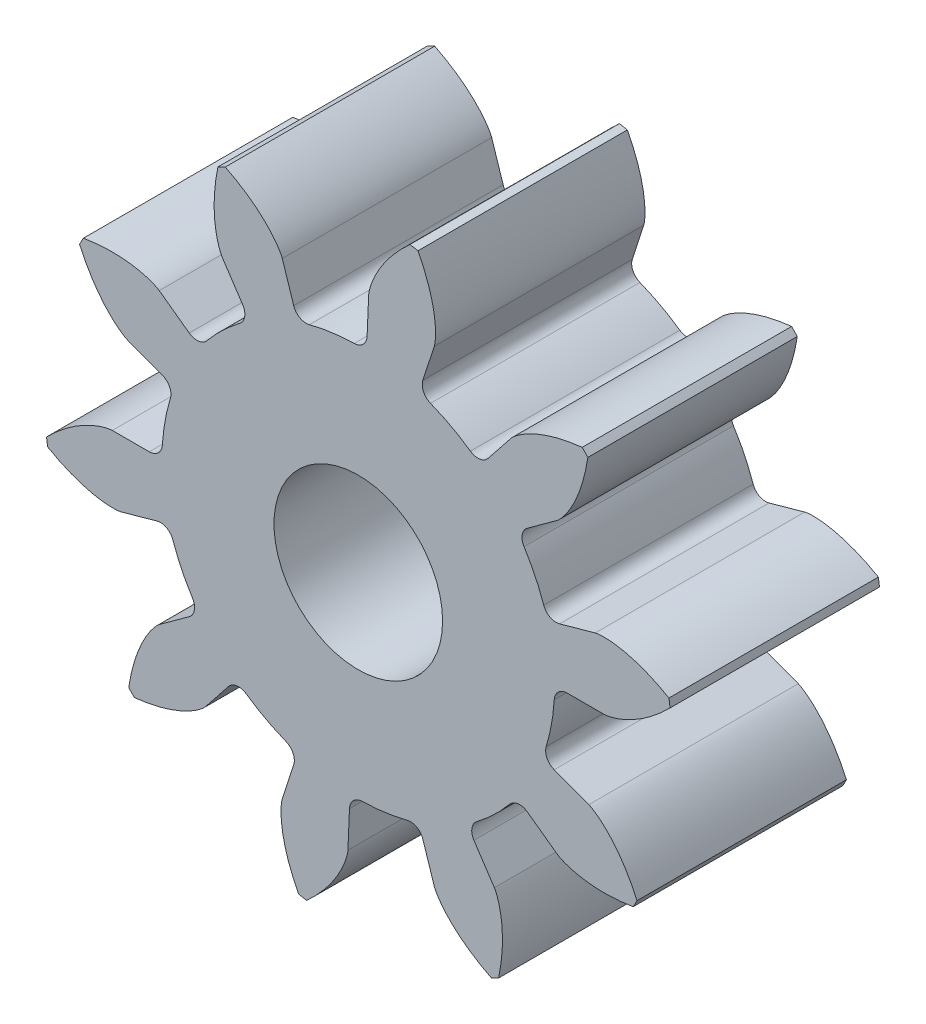
SolidWorks part; units mm, degrees
ref_plane "Front Plane" through (0, 0, 0) normal (0, 0, 1) x (1, 0, 0)
ref_plane "Top Plane" through (0, 0, 0) normal (0, 1, 0) x (1, 0, 0)
ref_plane "Right Plane" through (0, 0, 0) normal (1, 0, 0) x (0, 0, -1)
sketch "Sketch1" plane through (0, 0, 0) normal (0, 0, 1) x (1, 0, 0)
  line L0 (11.7462, 0) -> (9.375, 0)
  line L1 (14.8615, 2.0335) -> (-14.8615, -2.0335)
  line L2 (0, 0) -> (12.4986, 0.1863) construction
  circle A0 centre (0, 0) radius 11.7462 construction
  circle A1 centre (0, 0) radius 15
  circle A2 centre (0, 0) radius 9.375
  circle A3 centre (0, 0) radius 12.5 construction
  spline S0 degree 4 poles (11.7462, 0) (11.7548, 0.0002) (11.7792, 0.0013) (11.8251, 0.0056) (11.8997, 0.0157) (11.9942, 0.0334) (12.1154, 0.0615) (12.2568, 0.1013) (12.4106, 0.1522) (12.5757, 0.215) (12.7384, 0.2842) (12.8986, 0.3593) (13.0561, 0.4395) (13.2442, 0.5429) (13.4661, 0.6756) (13.7194, 0.8429) (13.9992, 1.0471) (14.2756, 1.27) (14.5402, 1.5014) (14.7983, 1.7485) (15.0415, 1.9969) (15.284, 2.2678) (15.5027, 2.5246) (15.7358, 2.8258) (15.9205, 3.0729) (16.1508, 3.4126) (16.2828, 3.6172) (16.4326, 3.8613) (16.4966, 3.972) (16.5361, 4.0402) knots 0 0 0 0 0 0.005377 0.015084 0.028532 0.04661 0.064855 0.092111 0.119476 0.146842 0.174209 0.201575 0.228941 0.256307 0.307035 0.361767 0.4165 0.471232 0.525964 0.580697 0.635429 0.690161 0.744894 0.799626 0.854358 0.909091 0.954545 1 1 1 1 1 construction
  spline S1 degree 4 poles (11.7462, 0) (11.7548, 0.0002) (11.7792, 0.0013) (11.8251, 0.0056) (11.8997, 0.0157) (11.9942, 0.0334) (12.1154, 0.0615) (12.2568, 0.1013) (12.4106, 0.1522) (12.5757, 0.215) (12.7384, 0.2842) (12.8986, 0.3593) (13.0561, 0.4395) (13.2442, 0.5429) (13.4661, 0.6756) (13.7194, 0.8429) (13.9992, 1.0471) (14.2756, 1.27) (14.5402, 1.5014) (14.7983, 1.7485) (15.0415, 1.9969) (15.284, 2.2678) (15.5027, 2.5246) (15.7358, 2.8258) (15.9205, 3.0729) (16.1009, 3.3389) (16.1871, 3.47) (16.2305, 3.5376) knots 0 0 0 0 0 0.005377 0.015084 0.028532 0.04661 0.064855 0.092111 0.119476 0.146842 0.174209 0.201575 0.228941 0.256307 0.307035 0.361767 0.4165 0.471232 0.525964 0.580697 0.635429 0.690161 0.744894 0.799626 0.854358 0.909091 0.909091 0.909091 0.909091 0.909091
  dimension "D1" = 23.4923
  dimension "D2" = 30
  dimension "D3" = 18.75
  dimension "D5" = 25
  dimension "D4" = 6.937
extrude "Boss-Extrude3" add sketch "Sketch1" along normal blind 10 contours L1 A2 | A2 L1 | L0 S1 A1 L1 A2
mirror "Mirror2" about plane through (0, 0, 10) normal (0.1356, -0.9908, 0) of "Boss-Extrude3"
fillet "Fillet1" radius 0.625 2 edges at (9.0304, 2.5184, 5) (9.375, 0, 5)
pattern_circular "CirPattern8" count 10 over 360 about axis through (0, 0, 10) along (0, 0, -1) of "Boss-Extrude3", "Mirror2", "Fillet1"
sketch "Sketch3" plane through (0, 0, 10) normal (0, 0, 1) x (1, 0, 0)
  circle A0 centre (0, 0) radius 4.025
  dimension "D1" = 8.05
extrude "Cut-Extrude2" cut sketch "Sketch3" against normal through all
equation "\"d\"= 25mm'Pitch diameter"
equation "\"N\"= 10'Number of teeth"
equation "\"bl\"= 0.9mm'Backlash"
equation "\"pa\"= 20deg'Pressure angle (deg)"
equation "\"pc\"= ( 3.1415 * \"d\" ) / \"N\"\t'Circular pitch"
equation "\"m\"= \"d\" / \"N\"\t\t\t'module"
equation "\"P\"= \"N\" / \"d\"\t\t\t'Diametral pitch"
equation "\"a\"= 1/\"P\"\t\t\t'Addendum distance"
equation "\"b\"= 1.25 / \"P\"'Dedendum distance"
equation "\"rb\"= (\"d\"/2)*cos(\"pa\")\t\t'base circle radius"
equation "\"cp\"= 3.1415/\"P\"\t\t'Circular pitch"
equation "\"t\"= ( \"cp\" / 2 ) - \"bl\"'tooth tickness"
equation "\"c\"=\"b\"-\"a\"\t\t\t'Clearance"
equation "\"facewidth\"= 10mm'face width"
equation "\"rbd\"= \"rb\" * 2'base circle diameter"
equation "\"D1@Sketch1\"=\"rbd\""
equation "\"D2@Sketch1\"= \"d\" + (\"a\" * 2)"
equation "\"D3@Sketch1\" = \"ded\""
equation "\"D4@Sketch1\"= ((\"t\" /2) / (\"d\"/2)) * (180/3.1415)"
equation "\"D1@Boss-Extrude3\"=\"facewidth\""
equation "\"D1@Fillet1\"=\"c\""
equation "\"D1@CirPattern8\"=\"N\""
equation "\"D5@Sketch1\"=\"d\""
equation "\"ded1\"= \"d\" - 2 * ( ( ( \"d\" / 2 ) - \"rb\" ) + ( 0.5 * ( 1.25 / \"P\" ) ) )"
equation "\"ded2\"= \"d\" - ( \"b\" * 2 )"
equation "\"ded\"= IIF ( \"rb\" < ( \"ded2\" / 2 ) , \"ded1\" , \"ded2\" )"
equation "\"shaftdia\"= 8.05mm"
equation "\"D1@Sketch3\"=\"shaftdia\""
